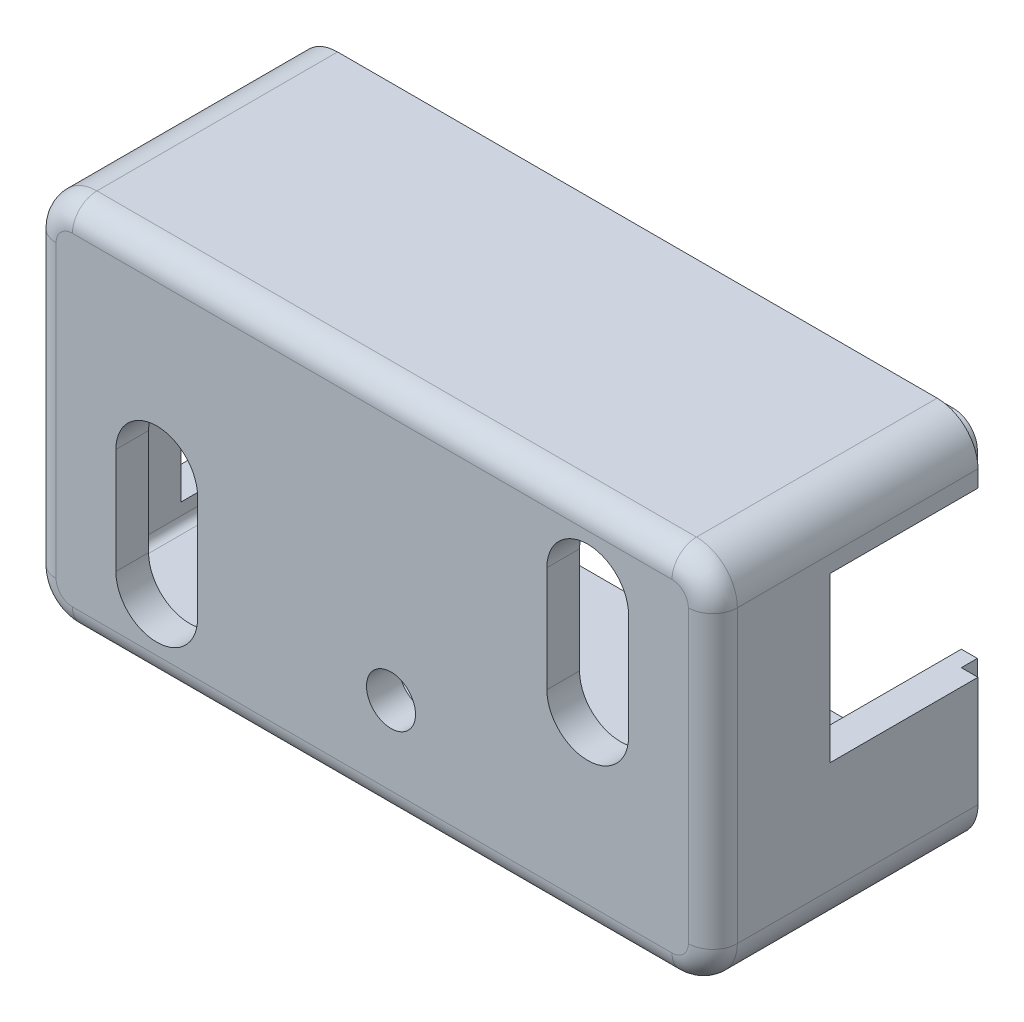
SolidWorks part; units mm, degrees
ref_plane "Front Plane" through (0, 0, 0) normal (0, 0, 1) x (1, 0, 0)
ref_plane "Top Plane" through (0, 0, 0) normal (0, 1, 0) x (1, 0, 0)
ref_plane "Right Plane" through (0, 0, 0) normal (1, 0, 0) x (0, 0, -1)
sketch "Sketch1" plane through (0, 0, 0) normal (0, 0, 1) x (1, 0, 0)
  line L0 (0, 0) -> (-35.7, 0) construction
  line L1 (3, -3) -> (-38.7, -3)
  line L2 (3, -3) -> (3, 19.8)
  line L3 (3, 19.8) -> (-38.7, 19.8)
  line L4 (-38.7, -3) -> (-38.7, 19.8)
  line L5 (3, -3) -> (-38.7, 19.8) construction
  line L6 (3, 19.8) -> (-38.7, -3) construction
  line L7 (0, 16.8) -> (0, 0) construction
  line L8 (-35.7, 0) -> (-35.7, 16.8) construction
  line L9 (-35.7, 16.8) -> (0, 16.8) construction
  point P0 (-17.85, 8.4)
  dimension "D1" = 3
  dimension "D2" = 3
  dimension "D3" = 3
  dimension "D4" = 3
extrude "Boss-Extrude1" add sketch "Sketch1" along normal blind 16 and the other way blind 6 contours L4 L3 L2 L1
sketch "Sketch5" plane through (0, 0, 0) normal (0, 1, 0) x (1, 0, 0)
  line L0 (11.5277, 0.23) -> (-46.7482, 0.23)
  line L1 (3, -16) -> (-38.7, -16) construction
  dimension "D1" = 16.23
fillet "Fillet1" radius 2.5 4 edges at (3, 19.8, 5) (3, -3, 5) (-38.7, 19.8, 5) (-38.7, -3, 5)
shell "Shell1" thickness 2
fillet "Fillet2" radius 1.5 8 edges at (2.2678, -2.2678, 16) (3, 8.4, 16) (2.2678, 19.0678, 16) (-17.85, 19.8, 16) (-37.9678, 19.0678, 16) (-38.7, 8.4, 16) (-37.9678, -2.2678, 16) (-17.85, -3, 16)
split "Split2" trim tools "Sketch5" bodies to split 101 resulting bodies 104 105
sketch "Sketch6" plane through (0, -3, 0) normal (0, -1, 0) x (1, 0, 0)
  line L5 (-36.2, 16) -> (0.5, 16) construction
  line L6 (-45.3217, -10.4186) -> (6.5133, -10.4186)
  line L7 (-45.3217, -10.4186) -> (-45.3217, -0.23)
  line L8 (-45.3217, -0.23) -> (6.5133, -0.23)
  line L9 (6.5133, -10.4186) -> (6.5133, -0.23)
  dimension "D1" = 16.23
extrude "Cut-Extrude1" cut sketch "Sketch6" against normal blind 25
sketch "Sketch7" plane through (0, 0, -0.23) normal (0, 0, -1) x (-1, 0, 0)
  line L0 (-0.5, -1) -> (36.2, -1) construction
  line L1 (-1, -0.5) -> (-1, 17.3) construction
  line L2 (-0.5, 17.8) -> (36.2, 17.8) construction
  line L3 (36.7, -0.5) -> (36.7, 17.3) construction
  line L4 (-0.5, -1) -> (36.2, -1)
  line L5 (-1, -0.5) -> (-1, 17.3)
  line L6 (-0.5, 17.8) -> (36.2, 17.8)
  line L7 (36.7, -0.5) -> (36.7, 17.3)
  line L8 (-0.5, -1.98) -> (36.2, -1.98)
  line L9 (37.68, -0.5) -> (37.68, 17.3)
  line L10 (-0.5, 18.78) -> (36.2, 18.78)
  line L11 (-1.98, -0.5) -> (-1.98, 17.3)
  arc A0 (36.2, -1) -> (36.7, -0.5) centre (36.2, -0.5) ccw construction
  arc A1 (-1, -0.5) -> (-0.5, -1) centre (-0.5, -0.5) ccw construction
  arc A2 (-0.5, 17.8) -> (-1, 17.3) centre (-0.5, 17.3) ccw construction
  arc A3 (36.7, 17.3) -> (36.2, 17.8) centre (36.2, 17.3) ccw construction
  arc A4 (36.2, -1) -> (36.7, -0.5) centre (36.2, -0.5) ccw
  arc A5 (-1, -0.5) -> (-0.5, -1) centre (-0.5, -0.5) ccw
  arc A6 (-0.5, 17.8) -> (-1, 17.3) centre (-0.5, 17.3) ccw
  arc A7 (36.7, 17.3) -> (36.2, 17.8) centre (36.2, 17.3) ccw
  arc A8 (36.2, -1.98) -> (37.68, -0.5) centre (36.2, -0.5) ccw
  arc A9 (37.68, 17.3) -> (36.2, 18.78) centre (36.2, 17.3) ccw
  arc A10 (-0.5, 18.78) -> (-1.98, 17.3) centre (-0.5, 17.3) ccw
  arc A11 (-1.98, -0.5) -> (-0.5, -1.98) centre (-0.5, -0.5) ccw
  dimension "D1" = 0.98
extrude "Boss-Extrude2" add sketch "Sketch7" along normal blind 0.98
sketch "Sketch8" plane through (0, 0, 16) normal (0, 0, 1) x (1, 0, 0)
  line L0 (-4.66, 15.0934) -> (-4.66, 8.6279) construction
  line L1 (-2.16, 15.0934) -> (-2.16, 8.6279)
  line L2 (-7.16, 15.0934) -> (-7.16, 8.6279)
  line L3 (3, 17.3) -> (3, -0.5) construction
  line L4 (1.5, 8.4) -> (-37.2, 8.4) construction
  line L5 (1.5, -0.5) -> (1.5, 17.3) construction
  line L6 (-37.2, 17.3) -> (-37.2, -0.5) construction
  line L7 (-17.85, 8.4) -> (-17.85, -1.5) construction
  line L8 (-36.2, -1.5) -> (0.5, -1.5) construction
  line L9 (-31.04, 10.6721) -> (-31.04, 8.6279) construction
  line L12 (-31.04, 1.7066) -> (-31.04, 8.1721) construction
  line L13 (-33.54, 1.7066) -> (-33.54, 8.1721)
  line L14 (-28.54, 1.7066) -> (-28.54, 8.1721)
  arc A0 (-2.16, 15.0934) -> (-7.16, 15.0934) centre (-4.66, 15.0934) ccw
  arc A1 (-7.16, 8.6279) -> (-2.16, 8.6279) centre (-4.66, 8.6279) ccw
  arc A4 (-33.54, 1.7066) -> (-28.54, 1.7066) centre (-31.04, 1.7066) ccw
  arc A5 (-28.54, 8.1721) -> (-33.54, 8.1721) centre (-31.04, 8.1721) ccw
  point P2 (-4.66, 11.8606)
  point P21 (-31.04, 11.8606)
  point P28 (-31.04, 4.9394)
  dimension "D1" = 7.66
  dimension "D2" = 5
extrude "Cut-Extrude2" cut sketch "Sketch8" against normal blind 11
sketch "Sketch9" plane through (3, 0, 0) normal (1, 0, 0) x (0, 0, -1)
  line L1 (2.4922, 16.2807) -> (-8.8434, 16.2807)
  line L2 (2.4922, 16.2807) -> (2.4922, 6.2525)
  line L3 (2.4922, 6.2525) -> (-8.8434, 6.2525)
  line L4 (-8.8434, 16.2807) -> (-8.8434, 6.2525)
extrude "Cut-Extrude3" cut sketch "Sketch9" against normal blind 11
sketch "Sketch10" plane through (-38.7, 0, 0) normal (-1, 0, 0) x (0, 0, 1)
  line L0 (8.8434, 16.2807) -> (8.8434, 6.2525) construction
  line L1 (-2.1657, 0.2351) -> (8.8434, 0.2351)
  line L2 (-2.1657, 0.2351) -> (-2.1657, 10.3313)
  line L3 (-2.1657, 10.3313) -> (8.8434, 10.3313)
  line L4 (8.8434, 0.2351) -> (8.8434, 10.3313)
extrude "Cut-Extrude4" cut sketch "Sketch10" against normal blind 11
sketch "Sketch11" plane through (0, 0, 16) normal (0, 0, 1) x (1, 0, 0)
  line L0 (3, 17.3) -> (3, -0.5) construction
  line L1 (0.5, -3) -> (-36.2, -3) construction
  circle A0 centre (-16.7, 3.3) radius 1.5
  point P4 (0, 0)
  dimension "D2" = 3
  dimension "D1" = 19.7
  dimension "D3" = 6.3
extrude "Cut-Extrude5" cut sketch "Sketch11" against normal blind 11
